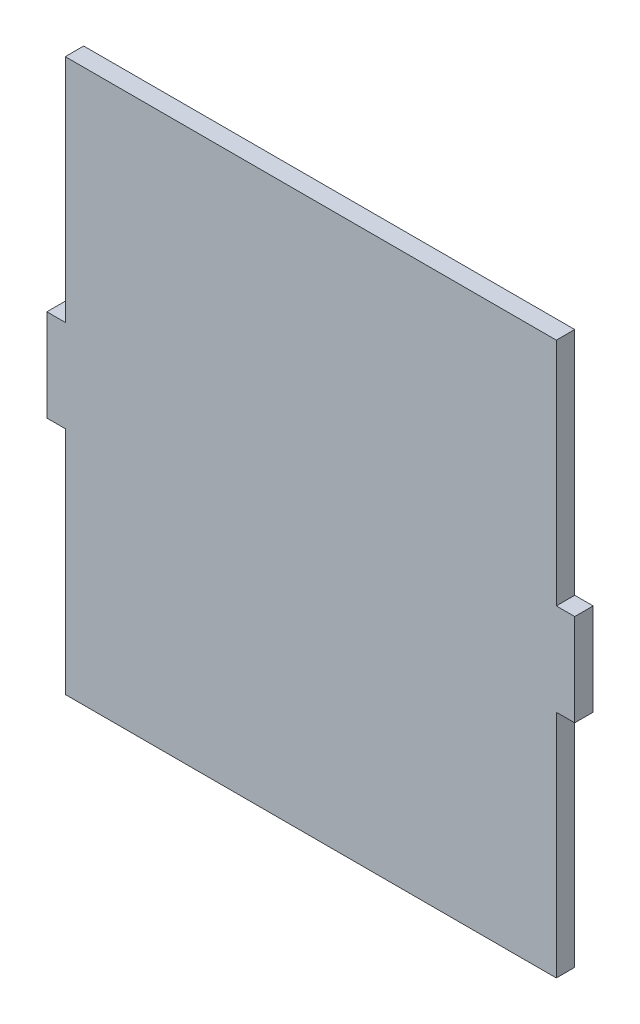
SolidWorks part; units mm, degrees
ref_plane "Front Plane" through (0, 0, 0) normal (0, 0, 1) x (1, 0, 0)
ref_plane "Top Plane" through (0, 0, 0) normal (0, 1, 0) x (1, 0, 0)
ref_plane "Right Plane" through (0, 0, 0) normal (1, 0, 0) x (0, 0, -1)
sketch "Sketch1" plane through (0, 0, 0) normal (0, 0, 1) x (1, 0, 0)
  line L0 (0, 0) -> (0, -45) construction
  line L1 (-40, 45) -> (40, 45)
  line L2 (-40, 45) -> (-40, -45)
  line L3 (-40, -45) -> (40, -45)
  line L4 (40, 45) -> (40, -45)
  line L5 (-40, 45) -> (40, -45) construction
  line L6 (-40, -45) -> (40, 45) construction
  line L7 (-40, 7.5) -> (-43, 7.5)
  line L8 (-40, 7.5) -> (-40, -7.5)
  line L9 (-40, -7.5) -> (-43, -7.5)
  line L10 (-43, 7.5) -> (-43, -7.5)
  line L11 (40, -7.5) -> (43, -7.5)
  line L12 (43, 7.5) -> (43, -7.5)
  line L13 (40, 7.5) -> (43, 7.5)
  line L14 (40, 7.5) -> (40, -7.5)
  point P0 (0, 0)
  dimension "D1" = 90
  dimension "D2" = 80
  dimension "D3" = 37.5
  dimension "D4" = 15
  dimension "D5" = 3
extrude "Boss-Extrude1" add sketch "Sketch1" along normal blind 3 contours L7 L10 L9 L2 | L4 L1 L2 L3 | L13 L4 L11 L12
